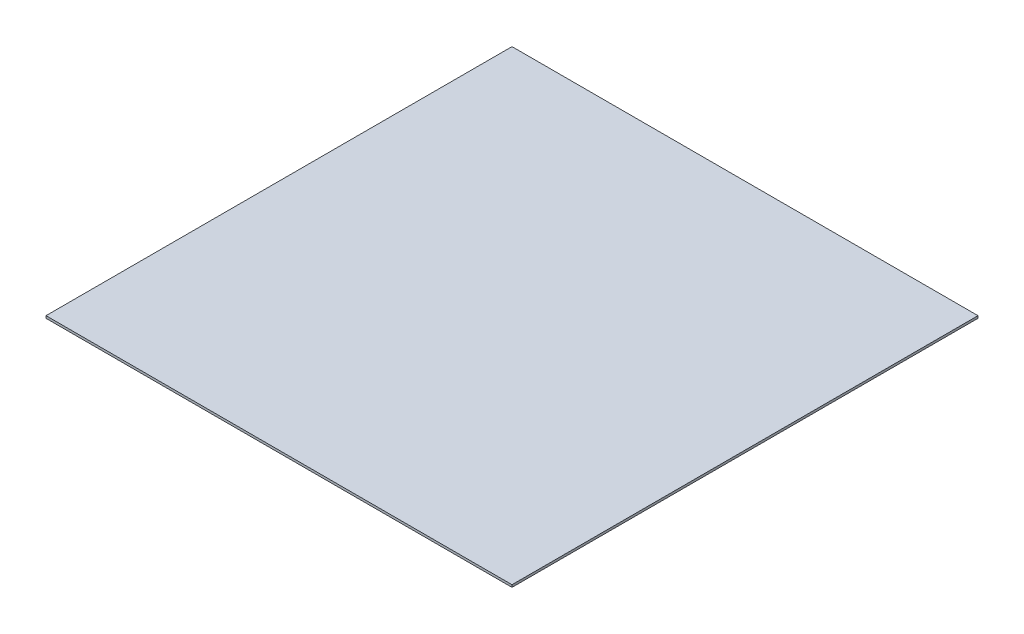
SolidWorks part; units mm, degrees
ref_plane "前视基准面" through (0, 0, 0) normal (0, 0, 1) x (1, 0, 0)
ref_plane "上视基准面" through (0, 0, 0) normal (0, 1, 0) x (1, 0, 0)
ref_plane "右视基准面" through (0, 0, 0) normal (1, 0, 0) x (0, 0, -1)
sketch "草图1" plane through (0, 0, 0) normal (0, 1, 0) x (1, 0, 0)
  line L0 (-100, 100) -> (100, 100)
  line L1 (-100, 100) -> (-100, -100)
  line L2 (100, 100) -> (100, -100)
  line L3 (-100, -100) -> (100, -100)
  line L4 (-100, 100) -> (100, -100) construction
  line L5 (100, 100) -> (-100, -100) construction
  point P1 (0, 0)
extrude "凸台-拉伸1" add sketch "草图1" along normal blind 1
